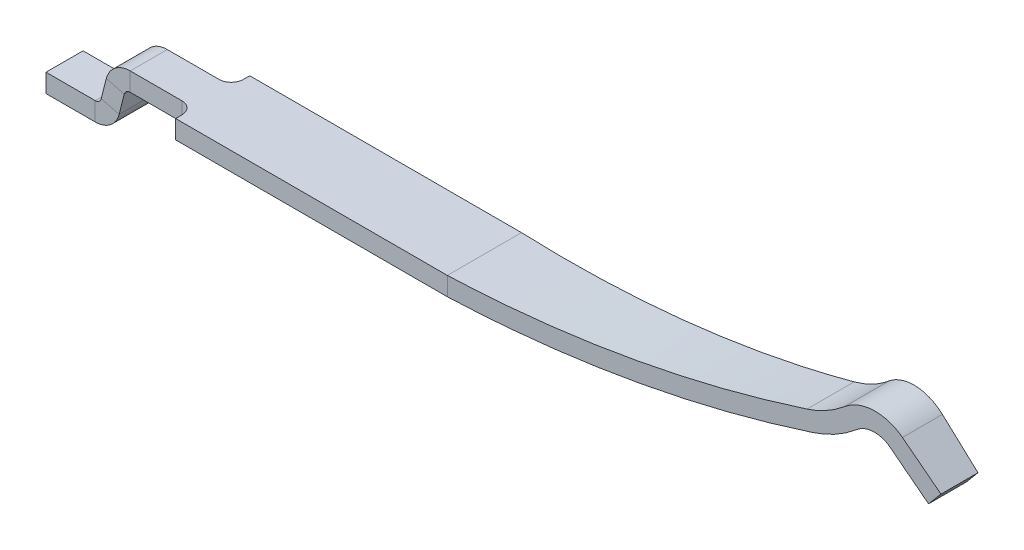
SolidWorks part; units mm, degrees
ref_plane "Front Plane" through (0, 0, 0) normal (0, 0, 1) x (1, 0, 0)
ref_plane "Top Plane" through (0, 0, 0) normal (0, 1, 0) x (1, 0, 0)
ref_plane "Right Plane" through (0, 0, 0) normal (1, 0, 0) x (0, 0, -1)
sketch "Sketch1" plane through (0, 0, 0) normal (1, 0, 0) x (0, 0, -1)
  line L1 (-0.3, 0.5) -> (0.3, 0.5)
  line L2 (-0.3, 0.5) -> (-0.3, 0.35)
  line L3 (-0.3, 0.35) -> (0.3, 0.35)
  line L4 (0.3, 0.5) -> (0.3, 0.35)
  line L5 (-0.3, 0.5) -> (0.3, 0.35) construction
  line L6 (-0.3, 0.35) -> (0.3, 0.5) construction
  point P0 (0, 0.425)
  dimension "D1" = 0.35
  dimension "D2" = 0.6
  dimension "D3" = 0.15
extrude "Boss-Extrude1" add sketch "Sketch1" along normal blind 1.7 contours L3 L4 L1 L2
sketch "Sketch2" plane through (0, 0, 0) normal (0, 1, 0) x (1, 0, 0)
  line L0 (0, 0) -> (-1.2, 0) construction
  dimension "D1" = 1.2
ref_plane "Plane1" through (-1.2, 0, 0) normal (1, 0, 0) x (0, 0, -1)
sketch "Sketch4" plane through (0, 0, 0) normal (0, 0, 1) x (1, 0, 0)
  line L0 (-1.2, 0) -> (-0.8017, 0)
  line L1 (0, 0) -> (-1.2, 0) construction
  line L2 (-1.2, -0.2475) -> (-1.2, 0.2475) construction
  line L3 (-0.5664, 0.3124) -> (-0.608, 0.1503)
  line L4 (-0.518, 0.35) -> (0, 0.35)
  arc A0 (-0.518, 0.35) -> (-0.5664, 0.3124) centre (-0.518, 0.3) ccw
  arc A1 (-0.608, 0.1503) -> (-0.8017, 0) centre (-0.8017, 0.2) cw
  dimension "D1" = 0.05
  dimension "D3" = 0.2
  dimension "D4" = 0.09
sketch "Sketch3" plane through (-1.2, 0, 0) normal (1, 0, 0) x (0, 0, -1)
  line L1 (0.15, 0.15) -> (-0.15, 0.15)
  line L2 (0.15, 0.15) -> (0.15, 0)
  line L3 (0.15, 0) -> (-0.15, 0)
  line L4 (-0.15, 0.15) -> (-0.15, 0)
  dimension "D1" = 0.3
  dimension "D2" = 0.15
sweep "Sweep1" add profiles "Sketch3" path "Sketch4"
fillet "Fillet1" radius 0.1 2 edges at (0, 0.425, -0.15) (0, 0.425, 0.15)
sketch "Sketch5" plane through (0, 0, 0) normal (0, 0, 1) x (1, 0, 0)
  line L0 (1.7, 0.35) -> (2.2, 0.35)
  line L1 (5.65, 0.9529) -> (5.95, 0.7)
  line L2 (-1.2, 0.15) -> (-1.2, 0) construction
  line L3 (0, 0) -> (5.95, 0) construction
  arc A0 (2.2, 0.35) -> (5.0464, 0.7661) centre (2.2, 10.294) ccw
  arc A1 (5.3922, 0.9529) -> (5.0464, 0.7661) centre (4.7702, 1.6907) cw
  arc A2 (5.3922, 0.9529) -> (5.65, 0.9529) centre (5.5211, 0.8) cw
  dimension "D5" = 0.2
  dimension "D1" = 7.15
  dimension "D2" = 0.3
  dimension "D3" = 0.5
  dimension "D4" = 1
  dimension "D8" = 0.7
sketch "Sketch6" plane through (1.7, 0, 0) normal (1, 0, 0) x (0, 0, -1)
  line L0 (-0.3, 0.5) -> (0.3, 0.5) construction
  line L1 (-0.3, 0.5) -> (-0.3, 0.35) construction
  line L2 (-0.3, 0.35) -> (0.3, 0.35) construction
  line L3 (0.3, 0.5) -> (0.3, 0.35) construction
  line L4 (-0.3, 0.5) -> (0.3, 0.5)
  line L5 (-0.3, 0.5) -> (-0.3, 0.35)
  line L6 (-0.3, 0.35) -> (0.3, 0.35)
  line L7 (0.3, 0.5) -> (0.3, 0.35)
sweep "Sweep2" add profiles "Sketch6" path "Sketch5"
sketch "Sketch8" plane through (0, 0, 0) normal (0, 1, 0) x (1, 0, 0)
  line L0 (-1.2, 0.4326) -> (6.0467, 0.15)
  line L1 (6.0467, 0.3) -> (6.0467, -0.3) construction
  line L2 (6.0467, 0.15) -> (6.0467, -0.15)
  line L3 (6.0467, -0.15) -> (-1.2, -0.4326)
  line L4 (-1.2, -0.4326) -> (-1.2, 0.4326)
  line L5 (-1.2, 0.15) -> (-1.2, -0.15) construction
  point P8 (6.0467, 0)
  dimension "D1" = 0.3
extrude "Cut-Extrude2" cut sketch "Sketch8" along normal through all flip side to cut
equation "\"pin_leg_start\" = 11.35"
equation "\"slot_offset\" = 2.9"
equation "\"pin_head_slot_offset\" = 1.2"
equation "\"pin_length\"= \"pin_leg_start\" - \"slot_offset\" - \"pin_head_slot_offset\""
equation "\"slot_length\" = 5"
equation "\"pin_leg_length\" = 1.8"
equation "\"D1@Sketch2\"=\"pin_leg_length\""
equation "\"D1@Sketch5\"=\"pin_length\""
